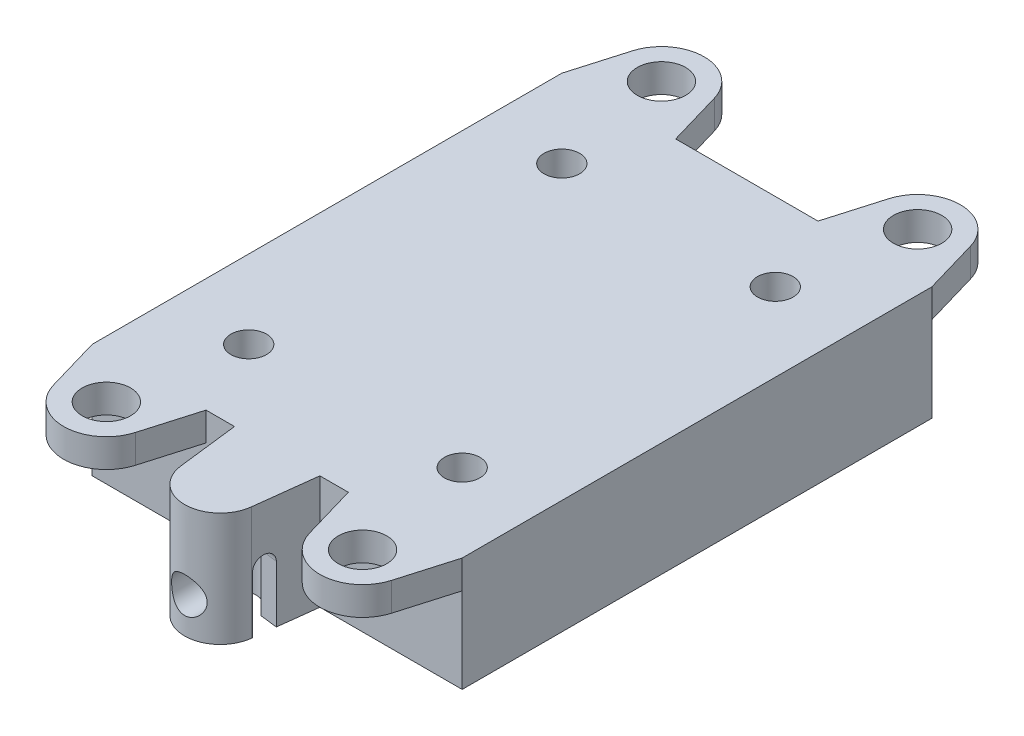
SolidWorks part; units mm, degrees
ref_plane "Front Plane" through (0, 0, 0) normal (0, 0, 1) x (1, 0, 0)
ref_plane "Top Plane" through (0, 0, 0) normal (0, 1, 0) x (1, 0, 0)
ref_plane "Right Plane" through (0, 0, 0) normal (1, 0, 0) x (0, 0, -1)
sketch "Sketch1" plane through (0, 0, 0) normal (0, 1, 0) x (1, 0, 0)
  line L0 (-2.4821, -4.299) -> (-3, 0)
  line L1 (-13, 33) -> (13, 33)
  line L2 (-13, 33) -> (-13, 0)
  line L3 (-13, 0) -> (-3, 0)
  line L4 (13, 33) -> (13, 0)
  line L5 (2.4821, -4.299) -> (3, 0)
  line L6 (3, 0) -> (13, 0)
  arc A0 (-2.4821, -4.299) -> (2.4821, -4.299) centre (0, -4) ccw
  dimension "D3" = 5
  dimension "D6" = 4
  dimension "D1" = 26
  dimension "D2" = 33
  dimension "D4" = 6
  dimension "D5" = 3
extrude "Boss-Extrude1" add sketch "Sketch1" along normal blind 8
sketch "Sketch2" plane through (0, 8, 0) normal (0, 1, 0) x (1, 0, 0)
  line L0 (-13, 16.5) -> (13, 16.5) construction
  line L1 (-13, 33) -> (-13, 0) construction
  line L2 (13, 0) -> (13, 33) construction
  line L3 (0, 33) -> (0, -9.541) construction
  line L4 (13, 33) -> (-13, 33) construction
  line L5 (-11.88, 36.84) -> (-13, 33)
  line L6 (-6.12, 36.84) -> (-5, 33)
  line L7 (-5, 33) -> (-13, 33)
  line L8 (5, 33) -> (13, 33)
  line L9 (6.12, 36.84) -> (5, 33)
  line L10 (11.88, 36.84) -> (13, 33)
  line L11 (-5, 0) -> (-13, 0)
  line L12 (-6.12, -3.84) -> (-5, 0)
  line L13 (-11.88, -3.84) -> (-13, 0)
  line L14 (11.88, -3.84) -> (13, 0)
  line L15 (6.12, -3.84) -> (5, 0)
  line L16 (5, 0) -> (13, 0)
  arc A0 (-6.12, 36.84) -> (-11.88, 36.84) centre (-9, 36) ccw
  arc A1 (6.12, 36.84) -> (11.88, 36.84) centre (9, 36) cw
  arc A2 (-6.12, -3.84) -> (-11.88, -3.84) centre (-9, -3) cw
  arc A3 (6.12, -3.84) -> (11.88, -3.84) centre (9, -3) ccw
  dimension "D1" = 6
  dimension "D2" = 3
  dimension "D3" = 4
extrude "Boss-Extrude2" add sketch "Sketch2" against normal blind 2
sketch "Sketch3" plane through (0, 0, 0) normal (0, -1, 0) x (1, 0, 0)
  line L0 (0, 0) -> (0, -4) construction
  line L1 (-11, -2) -> (11, -2)
  line L2 (-11, -2) -> (-11, -31)
  line L3 (-11, -31) -> (11, -31)
  line L4 (11, -2) -> (11, -31)
  line L5 (13, -16.5) -> (-13, -16.5) construction
  line L6 (13, 0) -> (13, -33) construction
  line L7 (-13, -33) -> (-13, 0) construction
  point P7 (0, -2)
  point P14 (-11, -16.5)
  dimension "D1" = 29
  dimension "D2" = 22
extrude "Cut-Extrude1" cut sketch "Sketch3" against normal blind 3
sketch "Sketch4" plane through (0, 0, 0) normal (0, -1, 0) x (-1, 0, 0)
  line L0 (0, 0) -> (0, -8.8942) construction
  circle A0 centre (0, -3) radius 1.5
  dimension "D1" = 3
  dimension "D2" = 3
extrude "Cut-Extrude2" cut sketch "Sketch4" against normal blind 5
hole_wizard "Tap Drill for M3x0.5 Tap1" positions "3DSketch1" profile "Sketch5" hole size "M3x0.5" standard "ANSI Metric"
sketch3d "3DSketch1"
  line L1 (0, 0, 6.5) -> (0, 9.9725, 6.5) construction
  line L3 (0, 0, 6.5) -> (-7.0757, 0, 6.5) construction
  arc A0 (-2.4821, 0, 4.299) -> (2.4821, 0, 4.299) centre (0, 0, 4) ccw construction
  point P0 (0, 2.5, 6.5)
  point P11 (0, 2.5, 4)
  dimension "D1" = 2.5
sketch "Sketch5" plane through (0, 2.5, 6.5) normal (1, 0, 0) x (0, -1, 0)
  line L0 (0, 0) -> (0, 2)
  line L1 (0, 2) -> (1.25, 2)
  line L2 (1.25, 2) -> (1.25, 0)
  line L5 (1.25, 0) -> (0, 0)
  line L11 (0, -6.35) -> (0, 107.95) construction
  dimension "Thru Hole Dia." = 2.5
  dimension "Thru Hole Depth" = 2
hole_wizard "M3 Clearance Hole1" positions "Sketch6" profile "Sketch7" hole size "M3" standard "ANSI Metric" end condition up to next
sketch "Sketch6" plane through (0, 6, 0) normal (0, -1, 0) x (-1, 0, 0)
  arc A0 (6.12, -3.84) -> (11.88, -3.84) centre (9, -3) ccw construction
  arc A1 (-11.88, -3.84) -> (-6.12, -3.84) centre (-9, -3) ccw construction
  arc A2 (11.88, 36.84) -> (6.12, 36.84) centre (9, 36) ccw construction
  arc A3 (-6.12, 36.84) -> (-11.88, 36.84) centre (-9, 36) ccw construction
  point P0 (9, -3)
  point P2 (-9, -3)
  point P4 (9, 36)
  point P6 (-9, 36)
sketch "Sketch7" plane through (-9, 6, 3) normal (1, 0, 0) x (0, 0, -1)
  line L0 (0, 0) -> (0, 2)
  line L1 (0, 2) -> (1.7, 2)
  line L2 (1.7, 2) -> (1.7, 0)
  line L5 (1.7, 0) -> (0, 0)
  line L11 (0, -6.35) -> (0, 107.95) construction
  dimension "Thru Hole Dia." = 3.4
  dimension "Thru Hole Depth" = 2
hole_wizard "Tap Drill for M3x0.5 Tap2" positions "Sketch8" profile "Sketch9" hole size "M3x0.5" standard "ANSI Metric" end condition up to next
sketch "Sketch8" plane through (0, 3, 0) normal (0, -1, 0) x (-1, 0, 0)
  line L0 (0, 2) -> (0, 31) construction
  line L1 (-11, 2) -> (11, 2) construction
  line L2 (11, 31) -> (-11, 31) construction
  line L4 (11, 16.5) -> (-11, 16.5) construction
  line L5 (11, 2) -> (11, 31) construction
  line L6 (-11, 31) -> (-11, 2) construction
  point P0 (7.5, 5.5)
  point P18 (7.5, 27.5)
  point P19 (-7.5, 27.5)
  point P20 (-7.5, 5.5)
  dimension "D1" = 7.5
  dimension "D2" = 11
sketch "Sketch9" plane through (-7.5, 3, -5.5) normal (1, 0, 0) x (0, 0, -1)
  line L0 (0, 0) -> (0, 5)
  line L1 (0, 5) -> (1.25, 5)
  line L2 (1.25, 5) -> (1.25, 0)
  line L5 (1.25, 0) -> (0, 0)
  line L11 (0, -6.35) -> (0, 107.95) construction
  dimension "Thru Hole Dia." = 2.5
  dimension "Thru Hole Depth" = 5
sketch "Sketch10" plane through (0, 3, 0) normal (0, -1, 0) x (-1, 0, 0)
  line L0 (-11, 16.5) -> (11, 16.5) construction
  line L1 (-5, 10) -> (-9, 10)
  line L2 (-5, 10) -> (-5, 23)
  line L3 (-5, 23) -> (-9, 23)
  line L4 (-9, 10) -> (-9, 23)
  line L5 (-11, 31) -> (-11, 2) construction
  line L6 (11, 2) -> (11, 31) construction
  line L7 (-7.5, 27.5) -> (-7.5, 5.5) construction
  point P10 (-9, 16.5)
  dimension "D1" = 13
  dimension "D2" = 4
  dimension "D3" = 2
extrude "Cut-Extrude3" cut sketch "Sketch10" against normal blind 2
sketch "Sketch19" plane through (2.9571, 0, 0.3563) normal (0.9928, 0, 0.1196) x (0.1196, 0, -0.9928)
  line L0 (-2.3912, 0) -> (-2.3912, 4)
  line L1 (-3.9713, 0) -> (0.3588, 0) construction
  line L2 (-3.9713, 8) -> (0.3588, 8) construction
  line L3 (0.3588, 8) -> (0.3588, 0) construction
  line L4 (-3.8912, 4) -> (-3.8912, 0)
  line L5 (-3.8912, 0) -> (-2.3912, 0)
  circle A0 centre (-3.1412, 4) radius 0.75 construction
  arc A1 (-2.3912, 4) -> (-3.8912, 4) centre (-3.1412, 4) ccw
  dimension "D1" = 1.5
  dimension "D2" = 4
  dimension "D3" = 3.5
extrude "Cut-Extrude4" cut sketch "Sketch19" against normal up to next
